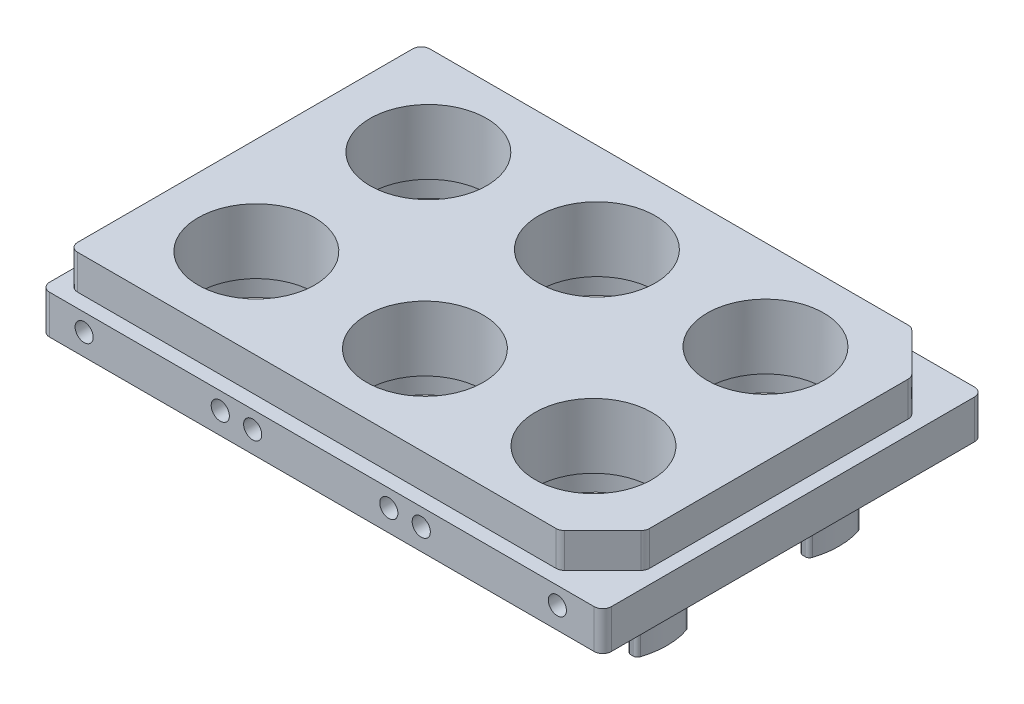
SolidWorks part; units mm, degrees
ref_plane "Front Plane" through (0, 0, 0) normal (0, 0, 1) x (1, 0, 0)
ref_plane "Top Plane" through (0, 0, 0) normal (0, 1, 0) x (1, 0, 0)
ref_plane "Right Plane" through (0, 0, 0) normal (1, 0, 0) x (0, 0, -1)
sketch "Sketch1" plane through (0, 0, 0) normal (0, 1, 0) x (1, 0, 0)
  line L1 (0, 0) -> (123.5, 0)
  line L2 (0, 0) -> (0, -81.5)
  line L3 (0, -81.5) -> (123.5, -81.5)
  line L4 (123.5, 0) -> (123.5, -81.5)
  dimension "D1" = 123.5
  dimension "D2" = 81.5
extrude "Boss-Extrude1" add sketch "Sketch1" along normal blind 8
chamfer "Chamfer1" distance 10 angle 45 2 edges at (123.5, 4, 81.5) (123.5, 4, 0)
sketch "Sketch2" plane through (0, 0, 0) normal (0, -1, 0) x (1, 0, 0)
  line L0 (0, 0) -> (0, 81.5) construction
  line L1 (-3.25, -3.25) -> (126.75, -3.25)
  line L2 (-3.25, -3.25) -> (-3.25, 84.75)
  line L3 (-3.25, 84.75) -> (126.75, 84.75)
  line L4 (126.75, -3.25) -> (126.75, 84.75)
  line L5 (113.5, 0) -> (0, 0) construction
  dimension "D1" = 88
  dimension "D2" = 130
  dimension "D3" = 3.25
  dimension "D4" = 3.25
extrude "Boss-Extrude2" add sketch "Sketch2" along normal blind 9
fillet "Fillet1" radius 2 10 edges at (113.5, 4, 0) (123.5, 4, 10) (123.5, 4, 71.5) (113.5, 4, 81.5) (126.75, -4.5, 84.75) (126.75, -4.5, -3.25) (-3.25, -4.5, -3.25) (0, 4, 0) (-3.25, -4.5, 84.75) (0, 4, 81.5)
sketch "Sketch3" plane through (0, -9, 0) normal (0, -1, 0) x (1, 0, 0)
  line L0 (-3.25, 82.75) -> (-3.25, -1.25) construction
  line L1 (-0.25, 81.75) -> (123.75, 81.75)
  line L2 (-0.25, 81.75) -> (-0.25, -0.25)
  line L3 (-0.25, -0.25) -> (123.75, -0.25)
  line L4 (123.75, 81.75) -> (123.75, -0.25)
  line L5 (-1.25, -3.25) -> (124.75, -3.25) construction
  dimension "D1" = 82
  dimension "D2" = 124
  dimension "D3" = 3
  dimension "D4" = 3
extrude "Cut-Extrude1" cut sketch "Sketch3" against normal blind 2
fillet "Fillet2" radius 2 4 edges at (123.75, -8, 81.75) (123.75, -8, -0.25) (-0.25, -8, -0.25) (-0.25, -8, 81.75)
sketch "Sketch4" plane through (0, 8, 0) normal (0, 1, 0) x (1, 0, 0)
  line L0 (-3.25, -82.75) -> (-3.25, 1.25) construction
  line L1 (112.6716, 0) -> (2, 0) construction
  line L2 (126.75, -40.75) -> (-3.25, -40.75) construction
  line L3 (126.75, 1.25) -> (126.75, -82.75) construction
  circle A0 centre (22.5, -20.85) radius 13.5
  circle A1 centre (61.5, -20.85) radius 13.5
  circle A2 centre (100.5, -20.85) radius 13.5
  circle A3 centre (100.5, -60.65) radius 13.5
  circle A4 centre (61.5, -60.65) radius 13.5
  circle A5 centre (22.5, -60.65) radius 13.5
  dimension "D1" = 25.75
  dimension "D2" = 39
  dimension "D3" = 39
  dimension "D4" = 20.85
  dimension "D5" = 27
extrude "Cut-Extrude2" cut sketch "Sketch4" against normal through all
sketch "Sketch5" plane through (0, -7, 0) normal (0, -1, 0) x (1, 0, 0)
  line L0 (126.75, 40.75) -> (-3.25, 40.75) construction
  line L1 (126.75, -1.25) -> (126.75, 82.75) construction
  line L2 (-3.25, 82.75) -> (-3.25, -1.25) construction
  circle A0 centre (22.5, 60.65) radius 14.5
  circle A1 centre (22.5, 60.65) radius 17
  circle A2 centre (61.5, 60.65) radius 14.5
  circle A3 centre (61.5, 60.65) radius 17
  circle A4 centre (100.5, 60.65) radius 14.5
  circle A5 centre (100.5, 60.65) radius 17
  circle A6 centre (100.5, 20.85) radius 17
  circle A7 centre (100.5, 20.85) radius 14.5
  circle A8 centre (61.5, 20.85) radius 17
  circle A9 centre (61.5, 20.85) radius 14.5
  circle A10 centre (22.5, 20.85) radius 17
  circle A11 centre (22.5, 20.85) radius 14.5
  dimension "D1" = 29
  dimension "D2" = 34
extrude "Boss-Extrude3" add sketch "Sketch5" along normal blind 16.5
sketch "Sketch6" plane through (0, -23.5, 0) normal (0, -1, 0) x (1, 0, 0)
  line L0 (100.5, 20.85) -> (142.0051, 20.85) construction
  line L1 (4.5, 26.85) -> (118.5, 26.85)
  line L2 (4.5, 26.85) -> (4.5, 14.85)
  line L3 (4.5, 14.85) -> (118.5, 14.85)
  line L4 (118.5, 26.85) -> (118.5, 14.85)
  line L5 (126.75, 40.75) -> (-3.25, 40.75) construction
  line L6 (-23.5, 39.1) -> (146.5, 39.1)
  line L7 (-23.5, 39.1) -> (-23.5, 2.6)
  line L8 (-23.5, 2.6) -> (146.5, 2.6)
  line L9 (146.5, 39.1) -> (146.5, 2.6)
  line L10 (-23.5, 39.1) -> (146.5, 2.6) construction
  line L11 (-23.5, 2.6) -> (146.5, 39.1) construction
  line L12 (126.75, -1.25) -> (126.75, 82.75) construction
  line L13 (-3.25, 82.75) -> (-3.25, -1.25) construction
  line L14 (-23.5, 78.9) -> (146.5, 42.4) construction
  line L15 (-23.5, 42.4) -> (146.5, 78.9) construction
  line L16 (100.5, 60.65) -> (142.0051, 60.65) construction
  line L17 (146.5, 42.4) -> (146.5, 78.9)
  line L18 (-23.5, 78.9) -> (146.5, 78.9)
  line L19 (-23.5, 42.4) -> (-23.5, 78.9)
  line L20 (-23.5, 42.4) -> (146.5, 42.4)
  line L21 (118.5, 54.65) -> (118.5, 66.65)
  line L22 (4.5, 66.65) -> (118.5, 66.65)
  line L23 (4.5, 54.65) -> (4.5, 66.65)
  line L24 (4.5, 54.65) -> (118.5, 54.65)
  circle A0 centre (22.5, 20.85) radius 13.5 construction
  point P11 (61.5, 20.85)
  point P31 (61.5, 60.65)
  dimension "D1" = 6
  dimension "D2" = 12
  dimension "D3" = 18
  dimension "D4" = 18
  dimension "D5" = 36.5
  dimension "D6" = 170
extrude "Cut-Extrude3" cut sketch "Sketch6" against normal blind 12
fillet "Fillet3" radius 1 48 edges at (6.594, -17.5, 66.65) (38.406, -17.5, 66.65) (35.7004, -17.5, 66.65) (9.2996, -17.5, 66.65) (9.2996, -17.5, 54.65) (35.7004, -17.5, 54.65) (6.594, -17.5, 54.65) (38.406, -17.5, 54.65) (74.7004, -17.5, 66.65) (48.2996, -17.5, 66.65) (45.594, -17.5, 66.65) (77.406, -17.5, 66.65) (48.2996, -17.5, 54.65) (74.7004, -17.5, 54.65) (45.594, -17.5, 54.65) (77.406, -17.5, 54.65) (113.7004, -17.5, 66.65) (87.2996, -17.5, 66.65) (84.594, -17.5, 66.65) (116.406, -17.5, 66.65) (87.2996, -17.5, 54.65) (113.7004, -17.5, 54.65) (84.594, -17.5, 54.65) (116.406, -17.5, 54.65) (113.7004, -17.5, 26.85) (87.2996, -17.5, 26.85) (116.406, -17.5, 26.85) (84.594, -17.5, 26.85) (116.406, -17.5, 14.85) (84.594, -17.5, 14.85) (87.2996, -17.5, 14.85) (113.7004, -17.5, 14.85) (48.2996, -17.5, 14.85) (74.7004, -17.5, 14.85) (77.406, -17.5, 14.85) (45.594, -17.5, 14.85) (77.406, -17.5, 26.85) (45.594, -17.5, 26.85) (74.7004, -17.5, 26.85) (48.2996, -17.5, 26.85) (38.406, -17.5, 26.85) (6.594, -17.5, 26.85) (35.7004, -17.5, 26.85) (9.2996, -17.5, 26.85) (38.406, -17.5, 14.85) (6.594, -17.5, 14.85) (9.2996, -17.5, 14.85) (35.7004, -17.5, 14.85)
sketch "Sketch7" plane through (0, -23.5, 0) normal (0, -1, 0) x (1, 0, 0)
  line L0 (22.5, 20.85) -> (9.8511, 20.85) construction
  line L1 (22.5, 20.85) -> (22.5, 13.7381) construction
  line L2 (22.5, 20.85) -> (61.5, 20.85) construction
  line L3 (42, 20.85) -> (42, 5.6594) construction
  line L4 (100.5, 20.85) -> (61.5, 20.85) construction
  line L5 (81, 20.85) -> (81, 5.6594) construction
  line L6 (126.75, 40.75) -> (-3.25, 40.75) construction
  line L7 (126.75, -1.25) -> (126.75, 82.75) construction
  line L8 (-3.25, 82.75) -> (-3.25, -1.25) construction
  circle A0 centre (6.75, 20.85) radius 0.85
  circle A1 centre (38.25, 20.85) radius 0.85
  circle A2 centre (45.75, 20.85) radius 0.85
  circle A3 centre (77.25, 20.85) radius 0.85
  circle A4 centre (84.75, 20.85) radius 0.85
  circle A5 centre (116.25, 20.85) radius 0.85
  circle A6 centre (116.25, 60.65) radius 0.85
  circle A7 centre (84.75, 60.65) radius 0.85
  circle A8 centre (77.25, 60.65) radius 0.85
  circle A9 centre (45.75, 60.65) radius 0.85
  circle A10 centre (38.25, 60.65) radius 0.85
  circle A11 centre (6.75, 60.65) radius 0.85
  dimension "D1" = 1.7
  dimension "D2" = 15.75
extrude "Cut-Extrude4" cut sketch "Sketch7" against normal blind 20.75
sketch "Sketch8" plane through (0, 0, 84.75) normal (0, 0, 1) x (1, 0, 0)
  line L0 (-3.25, -9) -> (-3.25, 0) construction
  line L1 (2, 0) -> (112.6716, 0) construction
  line L2 (38.25, -4) -> (45.75, -4) construction
  line L3 (42, -4) -> (42, 12.7019) construction
  line L4 (77.25, -4) -> (84.75, -4) construction
  line L5 (81, -4) -> (81, 14.8481) construction
  circle A0 centre (6.75, -4) radius 2.1
  circle A1 centre (38.25, -4) radius 2.1
  circle A2 centre (116.25, -4) radius 2.1
  circle A3 centre (77.25, -4) radius 2.1
  circle A4 centre (45.75, -4) radius 2.1
  circle A5 centre (84.75, -4) radius 2.1
  dimension "D1" = 10
  dimension "D2" = 4
  dimension "D3" = 4.2
  dimension "D4" = 31.5
  dimension "D5" = 7.5
  dimension "D6" = 7.5
extrude "Cut-Extrude5" cut sketch "Sketch8" against normal blind 26
sketch "Sketch9" plane through (0, 0, -3.25) normal (0, 0, -1) x (-1, 0, 0)
  circle A0 centre (-6.75, -4) radius 2.1
  circle A1 centre (-38.25, -4) radius 2.1
  circle A2 centre (-45.75, -4) radius 2.1
  circle A3 centre (-77.25, -4) radius 2.1
  circle A4 centre (-84.75, -4) radius 2.1
  circle A5 centre (-116.25, -4) radius 2.1
  dimension "D1" = 4.2
extrude "Cut-Extrude6" cut sketch "Sketch9" against normal blind 26
